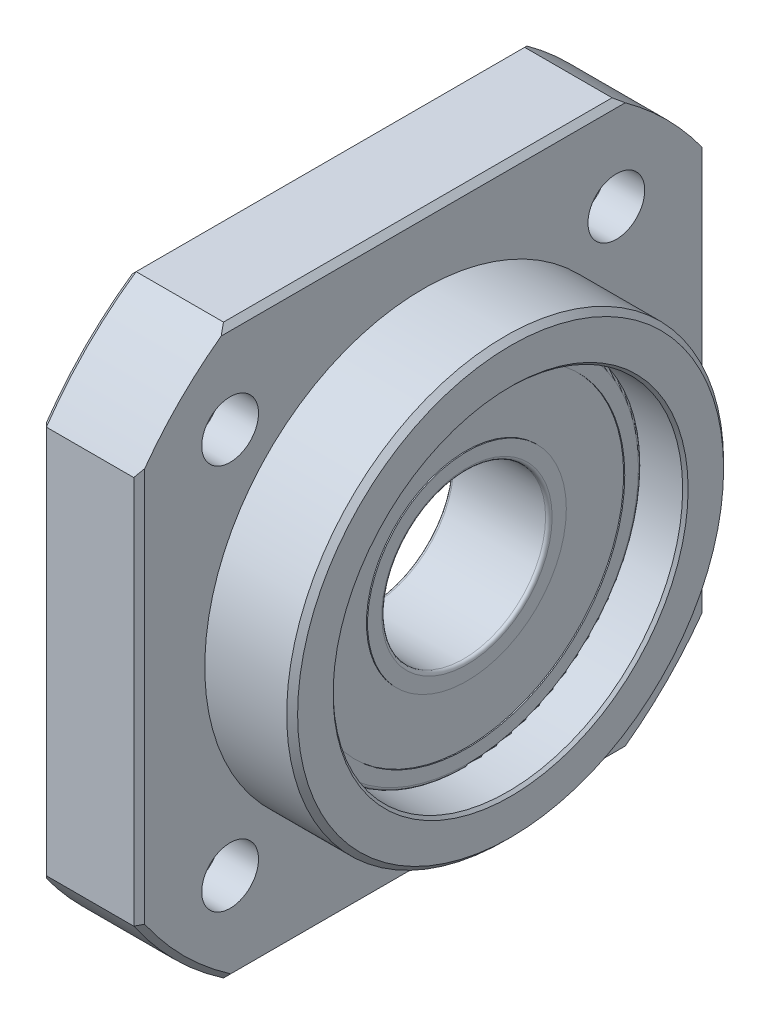
SolidWorks part; units mm, degrees
material "Unlegierter Baustahl"
ref_plane "Ebene vorne" through (0, 0, 0) normal (0, 0, 1) x (1, 0, 0)
ref_plane "Ebene oben" through (0, 0, 0) normal (0, 1, 0) x (1, 0, 0)
ref_plane "Ebene rechts" through (0, 0, 0) normal (1, 0, 0) x (0, 0, -1)
ref_plane "Ebene1" through (0, 0, 0) normal (1, 0, 0) x (0, 0, -1)
ref_plane "Ebene2" through (0, 0, 0) normal (0, 1, 0) x (1, 0, 0)
ref_plane "Ebene3" through (0, 0, 0) normal (0, 0, -1) x (-1, 0, 0)
sketch "Skizze1" plane through (0, 0, 0) normal (1, 0, 0) x (0, 0, -1)
  line L0 (-26, -26) -> (26, -26)
  line L1 (26, -26) -> (26, 26)
  line L2 (26, 26) -> (-26, 26)
  line L3 (-26, 26) -> (-26, -26)
extrude "Aufsatz-Linear austragen1" add sketch "Skizze1" along normal blind 17
sketch "Skizze2" plane through (0, 0, 0) normal (1, 0, 0) x (0, 0, -1)
  circle A0 centre (0, 0) radius 63
  circle A1 centre (0, 0) radius 31.5
extrude "Schnitt-Linear austragen1" cut sketch "Skizze2" along normal blind 17
ref_plane "Ebene4" through (9, 0, 0) normal (1, 0, 0) x (0, 0, -1)
sketch "Skizze3" plane through (9, 0, 0) normal (1, 0, 0) x (0, 0, -1)
  circle A0 centre (0, 0) radius 63
  circle A1 centre (0, 0) radius 20
extrude "Schnitt-Linear austragen2" cut sketch "Skizze3" along normal blind 8
ref_plane "Ebene5" through (0, 0, 0) normal (1, 0, 0) x (0, 0, -1)
sketch "Skizze4" plane through (0, 0, 0) normal (1, 0, 0) x (0, 0, -1)
  circle A0 centre (0, 0) radius 16
extrude "Schnitt-Linear austragen3" cut sketch "Skizze4" along normal blind 17
ref_plane "Ebene6" through (0, 0, 0) normal (1, 0, 0) x (0, 0, -1)
sketch "Skizze5" plane through (0, 0, 0) normal (1, 0, 0) x (0, 0, -1)
  circle A0 centre (-17.6777, 17.6777) radius 2.6
extrude "Schnitt-Linear austragen4" cut sketch "Skizze5" along normal blind 9
sketch "Skizze6" plane through (0, 0, 0) normal (1, 0, 0) x (0, 0, -1)
  line L0 (-17.6777, 17.6777) -> (17.6777, 17.6777)
  line L1 (-17.6777, 17.6777) -> (-17.6777, -17.6777)
pattern_linear "Lineares Muster1" count 2 spacing 35.3553 along (0, 0, -1) count 2 spacing 35.3553 along (0, -1, 0) of "Schnitt-Linear austragen4"
sketch "Skizze7" plane through (0, 0, 0) normal (1, 0, 0) x (0, 0, -1)
  circle A0 centre (-17.6777, 17.6777) radius 4.75
extrude "Schnitt-Linear austragen5" cut sketch "Skizze7" along normal blind 5.4
sketch "Skizze8" plane through (0, 0, 0) normal (1, 0, 0) x (0, 0, -1)
  line L0 (-17.6777, 17.6777) -> (17.6777, 17.6777)
  line L1 (-17.6777, 17.6777) -> (-17.6777, -17.6777)
pattern_linear "Lineares Muster2" count 2 spacing 35.3553 along (0, 0, -1) count 2 spacing 35.3553 along (0, -1, 0) of "Schnitt-Linear austragen5"
ref_plane "Ebene7" through (0, 0, 0) normal (0, 0, -1) x (-1, 0, 0)
sketch "Skizze9" plane through (0, 0, 0) normal (0, 0, -1) x (-1, 0, 0)
  line L0 (-13, 15.7) -> (-13, 14.45)
  line L1 (-13, 14.45) -> (-12.9, 14.45)
  line L2 (-12.9, 14.45) -> (-12.9, 9.1)
  line L3 (-12.9, 9.1) -> (-13, 9.1)
  line L4 (-13, 9.1) -> (-13, 7.8)
  line L5 (-12.7, 7.5) -> (-4.3, 7.5)
  line L6 (-4, 7.8) -> (-4, 9.1)
  line L7 (-4, 9.1) -> (-4.1, 9.1)
  line L8 (-4.1, 9.1) -> (-4.1, 14.45)
  line L9 (-4.1, 14.45) -> (-4, 14.45)
  line L10 (-4, 14.45) -> (-4, 15.7)
  line L11 (-4.3, 16) -> (-12.7, 16)
  line L12 (500, 0) -> (-500, 0) construction
  arc A0 (-13, 7.8) -> (-12.7, 7.5) centre (-12.7, 7.8) ccw
  arc A1 (-4.3, 7.5) -> (-4, 7.8) centre (-4.3, 7.8) ccw
  arc A2 (-4, 15.7) -> (-4.3, 16) centre (-4.3, 15.7) ccw
  arc A3 (-12.7, 16) -> (-13, 15.7) centre (-12.7, 15.7) ccw
revolve "Rotation1" add sketch "Skizze9" angle 360 about L12
chamfer "Fase1" distance 0.5 distance2 0.5 1 edges at (17, 0, -20)
chamfer "Fase2" distance 0.5 distance2 0.5 10 edges at (0, -26, 0) (0, 0, -26) (9, 0, 26) (9, -22.2739, 22.2739) (9, -26, 0) (9, 0, -26) (9, 26, 0) (0, 0, 26) (0, 26, 0) (0, 22.2739, 22.2739)
chamfer "Fase3" distance 0.25 distance2 0.25 2 edges at (17, 0, -16) (0, 0, -16)
sketch3d "3D-Skizze1"
  point P0 (0, -26, -26)
  point P1 (0, 26, 26)
  point P2 (0, -17.5163, 26)
  point P3 (0, -17.5163, -26)
  point P4 (0, -17.5163, 26)
  point P5 (0, 22.2739, 22.2739)
  point P6 (0, -22.2739, -22.2739)
  point P7 (0, 17.6777, -17.6777)
  point P8 (0, -17.6777, 17.6777)
  point P9 (0, -26, 0)
  point P10 (17, 26, 0)
  point P11 (-13.4167, -28.2, 0)
  point P12 (4.3, 7.5, 0)
  point P13 (4.3, -7.5, 0)
  point P14 (0, 25.5, 0)
  point P15 (17, 19.5, 0)
  point P16 (17, 19.5, 0)
  point P17 (9, 25.5, 0)
  point P18 (9, 25.5, 0)
  point P19 (0, 25.5, 0)
  point P20 (16.5, 20, 0)
  point P21 (16.5, -20, 0)
ref_plane "Ebene8" through (0, 0, 0) normal (1, 0, 0) x (0, 0, -1)
ref_plane "Ebene9" through (0, 0, 0) normal (0, 0, 1) x (1, 0, 0)
sketch "Skizze10" plane through (0, 0, 0) normal (1, 0, 0) x (0, 0, -1)
  point P0 (26, -17.5163)
  dimension "D1" = 52
  dimension "D2" = 63
  dimension "D3" = 50
sketch "Skizze11" plane through (0, 0, 0) normal (0, 0, 1) x (1, 0, 0)
  point P0 (4.3, 7.5)
  dimension "D1" = 15
  dimension "D2" = 17
  dimension "D3" = 8
  dimension "D4" = 9
  dimension "D5" = 40
sketch "Skizze13" plane through (9, 0, 0) normal (1, 0, 0) x (0, 0, -1)
  line L4 (-17.7834, 26) -> (17.7834, 26)
  line L5 (26, 17.7834) -> (26, -17.7834)
  line L6 (17.7834, -26) -> (-17.7834, -26)
  line L7 (-26, -17.7834) -> (-26, 17.7834)
  circle A0 centre (0, 0) radius 20
  circle A1 centre (-17.6777, 17.6777) radius 2.6
  circle A2 centre (17.6777, 17.6777) radius 2.6
  circle A3 centre (17.6777, -17.7749) radius 2.6
  circle A4 centre (-17.6777, -17.6777) radius 2.6
  arc A5 (-17.7834, 26) -> (-26, 17.7834) centre (0, 0) ccw
  arc A6 (26, 17.7834) -> (17.7834, 26) centre (0, 0) ccw
  arc A7 (17.7834, -26) -> (26, -17.7834) centre (0, 0) ccw
  arc A8 (-26, -17.7834) -> (-17.7834, -26) centre (0, 0) ccw
  dimension "D1" = 5.2
  dimension "D2" = 5.2
  dimension "D3" = 5.2
  dimension "D4" = 5.2
  dimension "D5" = 40
  dimension "D6" = 63
